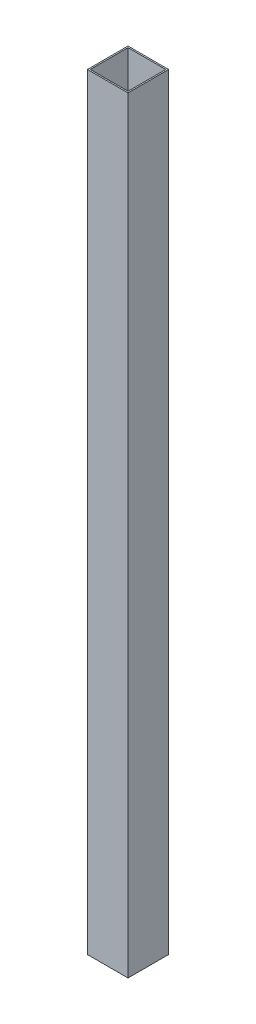
SolidWorks part; units mm, degrees
ref_plane "Front Plane" through (0, 0, 0) normal (0, 0, 1) x (1, 0, 0)
ref_plane "Top Plane" through (0, 0, 0) normal (0, 1, 0) x (1, 0, 0)
ref_plane "Right Plane" through (0, 0, 0) normal (1, 0, 0) x (0, 0, -1)
sketch "Sketch1" plane through (0, 0, 0) normal (0, 1, 0) x (1, 0, 0)
  line L0 (-11.811, -11.811) -> (11.811, -11.811)
  line L1 (-12.7, 12.7) -> (12.7, 12.7)
  line L2 (-12.7, 12.7) -> (-12.7, -12.7)
  line L3 (-12.7, -12.7) -> (12.7, -12.7)
  line L4 (12.7, 12.7) -> (12.7, -12.7)
  line L5 (-12.7, 12.7) -> (12.7, -12.7) construction
  line L6 (-12.7, -12.7) -> (12.7, 12.7) construction
  line L7 (11.811, 11.811) -> (11.811, -11.811)
  line L8 (-11.811, 11.811) -> (11.811, 11.811)
  line L9 (-11.811, 11.811) -> (-11.811, -11.811)
  point P0 (0, 0)
  dimension "D1" = 25.4
  dimension "D2" = 25.4
  dimension "D3" = 0.889
extrude "Boss-Extrude1" add sketch "Sketch1" along normal blind 479.425
